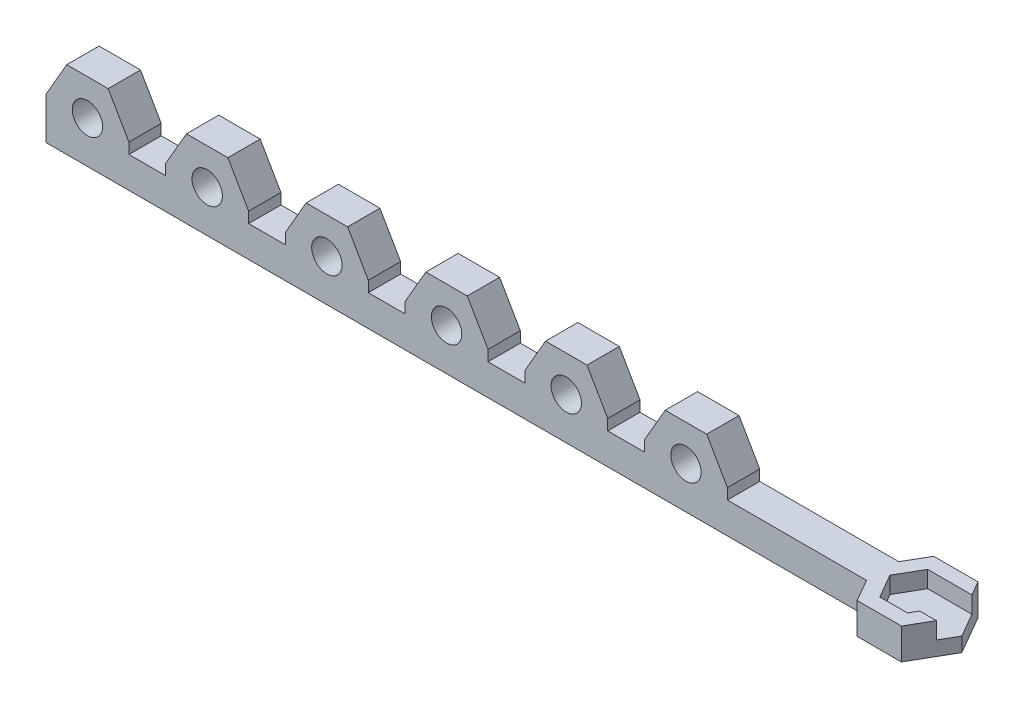
SolidWorks part; units mm, degrees
ref_plane "Front Plane" through (0, 0, 0) normal (0, 0, 1) x (1, 0, 0)
ref_plane "Top Plane" through (0, 0, 0) normal (0, 1, 0) x (1, 0, 0)
ref_plane "Right Plane" through (0, 0, 0) normal (1, 0, 0) x (0, 0, -1)
sketch "Sketch1" plane through (0, 0, 0) normal (0, 1, 0) x (1, 0, 0)
  line L1 (0, 0) -> (175, 0)
  line L2 (0, 0) -> (0, -6.75)
  line L3 (0, -6.75) -> (175, -6.75)
  line L4 (175, 0) -> (175, -6.75)
  dimension "D1" = 6.75
  dimension "D2" = 175
extrude "Boss-Extrude1" add sketch "Sketch1" along normal blind 6.5
sketch "Sketch2" plane through (0, 6.5, 0) normal (0, 1, 0) x (1, 0, 0)
  line L0 (175, 0) -> (0, 0) construction
  line L1 (0, 0) -> (10, 0)
  line L2 (0, 0) -> (0, -6.75)
  line L3 (0, -6.75) -> (10, -6.75)
  line L4 (10, 0) -> (10, -6.75)
  line L5 (0, -6.75) -> (175, -6.75) construction
  line L6 (0, 0) -> (0, -6.75) construction
  dimension "D1" = 10
extrude "Boss-Extrude2" add sketch "Sketch2" along normal blind 7.5
sketch "Sketch5" plane through (0, 0, 6.75) normal (0, 0, 1) x (1, 0, 0)
  line L1 (10, 14) -> (10, 6.5) construction
  circle A0 centre (5, 8.75) radius 3.175
  dimension "D3" = 6.35
  dimension "D1" = 8.75
  dimension "D2" = 5
extrude "Cut-Extrude2" cut sketch "Sketch5" against normal blind 10
ref_plane "Plane1" through (0, 0, 3.375) normal (0, 0, 1) x (1, 0, 0)
pattern_linear "LPattern1" count 6 spacing 25 along (1, 0, 0) of "Cut-Extrude2", "Boss-Extrude2"
sketch "Sketch6" plane through (0, 0, 6.75) normal (0, 0, 1) x (1, 0, 0)
  line L0 (138.6603, 8.75) -> (138.6603, 0)
  line L1 (138.6603, 8.75) -> (134.3301, 16.25)
  line L2 (134.3301, 16.25) -> (125.6699, 16.25)
  line L3 (125.6699, 16.25) -> (121.3397, 8.75)
  line L4 (121.3397, 8.75) -> (125.6699, 1.25) construction
  line L5 (125.6699, 1.25) -> (134.3301, 1.25) construction
  line L6 (134.3301, 1.25) -> (138.6603, 8.75) construction
  line L7 (0, 0) -> (175, 0) construction
  line L8 (121.3397, 8.75) -> (121.3397, 0)
  line L9 (121.3397, 0) -> (138.6603, 0)
  circle A0 centre (130, 8.75) radius 7.5 construction
  circle A1 centre (130, 8.75) radius 3.175
  circle A2 centre (130, 8.75) radius 3.175 construction
  dimension "D1" = 7.5
extrude "Boss-Extrude4" add sketch "Sketch6" against normal up to surface (6.75 mm away) up to face at (33.175, 8.75, 0)
pattern_linear "LPattern2" count 6 spacing 25 along (-1, 0, 0) of "Boss-Extrude4"
sketch "Sketch7" plane through (0, 6.5, 0) normal (0, 1, 0) x (1, 0, 0)
  line L0 (175, -6.75) -> (175, 0) construction
  line L1 (172.1132, -8.375) -> (177.8868, -8.375)
  line L2 (177.8868, -8.375) -> (180.7735, -3.375) construction
  line L3 (180.7735, -3.375) -> (177.8868, 1.625) construction
  line L4 (177.8868, 1.625) -> (172.1132, 1.625)
  line L5 (172.1132, 1.625) -> (169.2265, -3.375)
  line L6 (169.2265, -3.375) -> (172.1132, -8.375)
  line L7 (138.6603, -6.75) -> (175, -6.75) construction
  line L8 (179.6188, -11.375) -> (182.289, -6.75)
  line L9 (170.3812, -11.375) -> (179.6188, -11.375)
  line L10 (179.6188, -11.375) -> (184.2376, -3.375) construction
  line L11 (184.2376, -3.375) -> (179.6188, 4.625) construction
  line L12 (179.6188, 4.625) -> (170.3812, 4.625)
  line L13 (170.3812, 4.625) -> (165.7624, -3.375)
  line L14 (165.7624, -3.375) -> (170.3812, -11.375)
  line L15 (175, -6.75) -> (182.289, -6.75) construction
  line L16 (177.8868, -8.375) -> (178.8249, -6.75)
  line L17 (178.8249, -6.75) -> (182.289, -6.75)
  line L18 (177.8868, 1.625) -> (181.3509, 1.625)
  line L19 (181.3509, 1.625) -> (179.6188, 4.625)
  circle A0 centre (175, -3.375) radius 5 construction
  circle A1 centre (175, -3.375) radius 8 construction
  dimension "D1" = 5
  dimension "D2" = 8
extrude "Boss-Extrude5" add sketch "Sketch7" against normal blind 6.5
sketch "Sketch9" plane through (0, 0, 0) normal (0, -1, 0) x (-1, 0, 0)
  line L0 (-171.1751, 0) -> (-172.1132, 1.625) construction
  line L1 (-169.2265, -3.375) -> (-172.1132, 1.625)
  line L2 (-172.1132, 1.625) -> (-177.8868, 1.625)
  line L3 (-177.8868, 1.625) -> (-180.7735, -3.375) construction
  line L4 (-180.7735, -3.375) -> (-177.8868, -8.375) construction
  line L5 (-177.8868, -8.375) -> (-172.1132, -8.375)
  line L6 (-172.1132, -8.375) -> (-169.2265, -3.375)
  line L7 (-172.1132, -8.375) -> (-171.1751, -6.75) construction
  line L8 (-178.8249, -6.75) -> (-182.289, -6.75)
  line L9 (-182.289, -6.75) -> (-184.2376, -3.375)
  line L10 (-184.2376, -3.375) -> (-181.3509, 1.625)
  line L11 (-181.3509, 1.625) -> (-179.6188, 4.625) construction
  line L12 (-179.6188, -11.375) -> (-182.289, -6.75) construction
  line L13 (-177.8868, 1.625) -> (-181.3509, 1.625)
  line L14 (-178.8249, -6.75) -> (-177.8868, -8.375)
  circle A0 centre (-175, -3.375) radius 5 construction
extrude "Boss-Extrude6" add sketch "Sketch9" against normal blind 3
sketch "Sketch10" plane through (0, 0, 0) normal (0, -1, 0) x (-1, 0, 0)
  line L0 (-175, -11.375) -> (-175, 4.625) construction
  line L1 (-170.3812, -11.375) -> (-179.6188, -11.375) construction
  line L2 (-179.6188, 4.625) -> (-170.3812, 4.625) construction
  circle A1 centre (-175, -3.375) radius 2.55
  point P0 (-175, -3.375)
  dimension "D1" = 5.1
extrude "Cut-Extrude4" cut sketch "Sketch10" against normal blind 2
sketch "Sketch11" plane through (0, 3, 0) normal (0, 1, 0) x (1, 0, 0)
  line L0 (177.8868, -8.375) -> (172.1132, -8.375) construction
  line L1 (180.7735, -3.375) -> (177.8868, 1.625)
  line L2 (177.8868, 1.625) -> (172.1132, 1.625)
  line L3 (172.1132, 1.625) -> (169.2265, -3.375)
  line L4 (169.2265, -3.375) -> (172.1132, -8.375)
  line L5 (172.1132, -8.375) -> (177.8868, -8.375)
  line L6 (177.8868, -8.375) -> (180.7735, -3.375)
  line L7 (171.1751, 0) -> (172.1132, 1.625) construction
  circle A0 centre (175, -3.375) radius 5 construction
extrude "Cut-Extrude5" cut sketch "Sketch11" along normal blind 18
